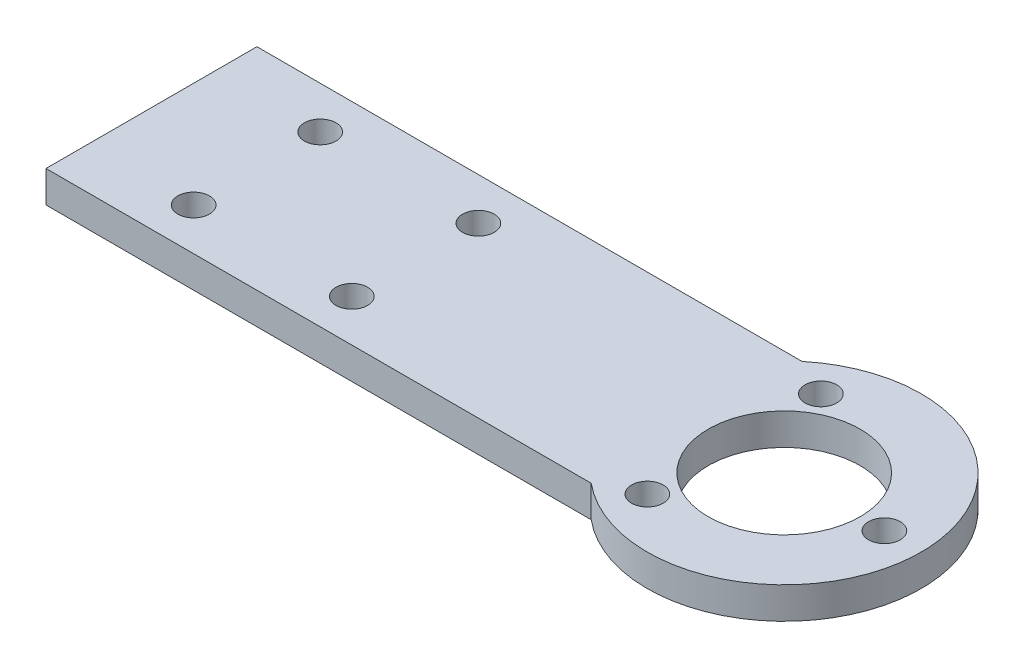
SolidWorks part; units mm, degrees
material "Thornel Mat VMA"
ref_plane "前视基准面" through (0, 0, 0) normal (0, 0, 1) x (1, 0, 0)
ref_plane "上视基准面" through (0, 0, 0) normal (0, 1, 0) x (1, 0, 0)
ref_plane "右视基准面" through (0, 0, 0) normal (1, 0, 0) x (0, 0, -1)
sketch "草图1" plane through (0, 0, 0) normal (0, 1, 0) x (1, 0, 0)
  line L1 (-58.5827, 11.5748) -> (-6.8893, 11.5748)
  line L2 (-58.5827, 11.5748) -> (-58.5827, -8.4252)
  line L3 (-58.5827, -8.4252) -> (-6.8893, -8.4252)
  circle A0 centre (-33.5827, 7.5748) radius 1.5
  circle A1 centre (-48.5827, 7.5748) radius 1.5
  circle A2 centre (-33.5827, -4.4252) radius 1.5
  circle A3 centre (-48.5827, -4.4252) radius 1.5
  circle A4 centre (1.4173, 1.5748) radius 7.2
  arc A6 (-6.8893, -8.4252) -> (-6.8893, 11.5748) centre (1.4173, 1.5748) ccw
  circle A7 centre (10.9173, 1.5748) radius 1.5
  circle A8 centre (-3.3327, -6.6524) radius 1.5
  circle A9 centre (-3.3327, 9.802) radius 1.5
  point P22 (1.4173, 1.5748)
  dimension "D2" = 4
  dimension "D3" = 25
  dimension "D4" = 15
  dimension "D5" = 12
  dimension "D6" = 60
  dimension "D7" = 9.5
  dimension "D1" = 20
  dimension "D8" = 3
extrude "凸台-拉伸1" add sketch "草图1" along normal blind 3
